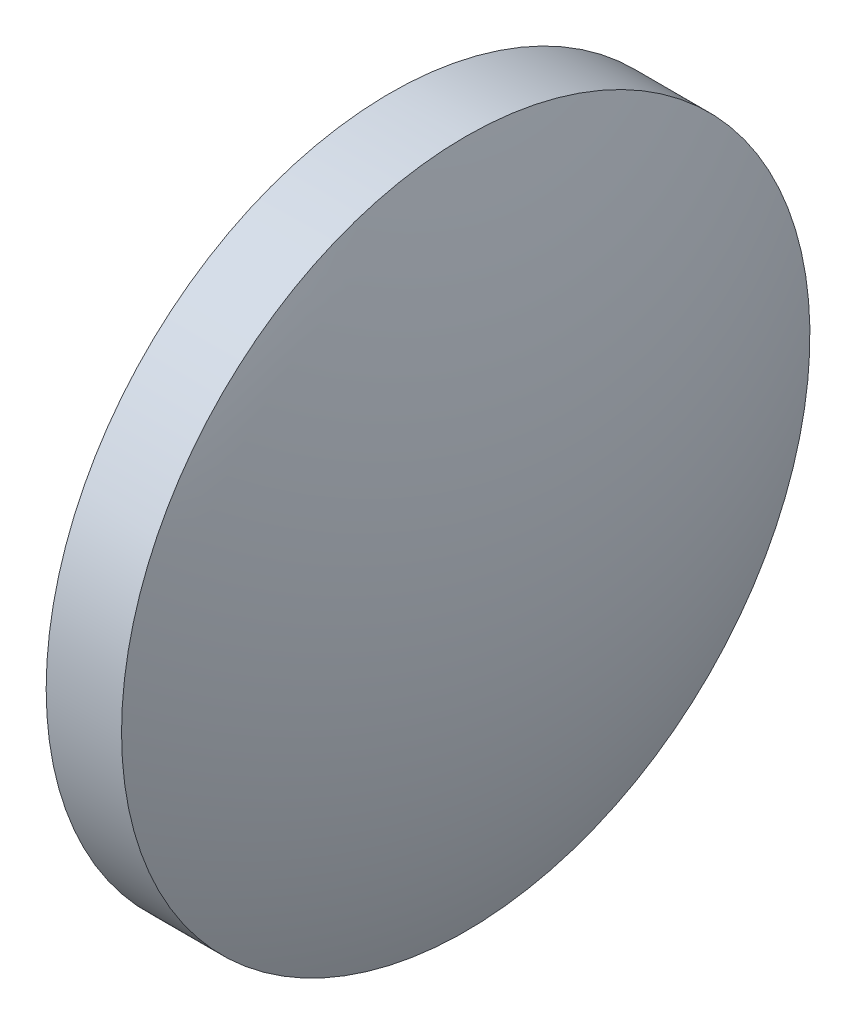
SolidWorks part; units mm, degrees
ref_plane "前视基准面" through (0, 0, 0) normal (0, 0, 1) x (1, 0, 0)
ref_plane "上视基准面" through (0, 0, 0) normal (0, 1, 0) x (1, 0, 0)
ref_plane "右视基准面" through (0, 0, 0) normal (1, 0, 0) x (0, 0, -1)
sketch "草图1" plane through (0, 0, 0) normal (0, 0, 1) x (1, 0, 0)
  line L0 (550.7365, 188.8612) -> (564.1823, 188.8612) construction
  line L1 (555.3931, 188.8612) -> (555.3931, 198.8612)
  line L2 (559.5931, 188.8612) -> (555.3931, 188.8612)
  line L5 (555.3931, 198.8612) -> (557.5831, 198.8612)
  arc A0 (559.5931, 188.8612) -> (557.5831, 198.8612) centre (533.7125, 188.8612) ccw
revolve "旋转1" add sketch "草图1" angle 360 about L0
